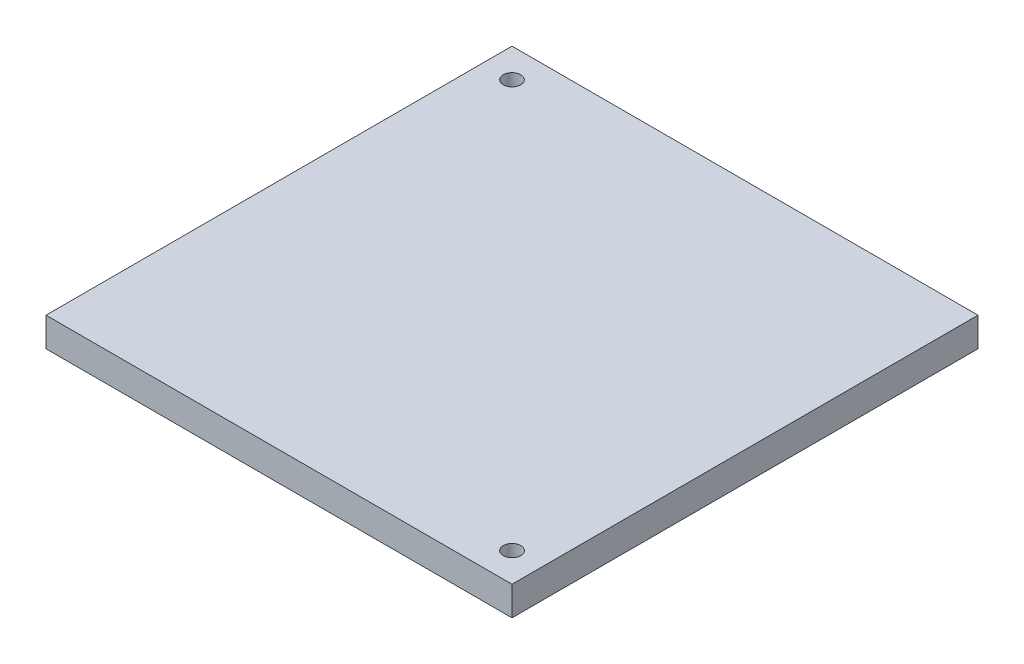
SolidWorks part; units mm, degrees
material "ABS PC"
ref_plane "Plan de face" through (0, 0, 0) normal (0, 0, 1) x (1, 0, 0)
ref_plane "Plan de dessus" through (0, 0, 0) normal (0, 1, 0) x (1, 0, 0)
ref_plane "Plan de droite" through (0, 0, 0) normal (1, 0, 0) x (0, 0, -1)
sketch "Esquisse1" plane through (0, 0, 0) normal (0, 1, 0) x (1, 0, 0)
  line L0 (-40, 40) -> (40, -40) construction
  line L1 (-40, 40) -> (40, 40)
  line L2 (-40, 40) -> (-40, -40)
  line L3 (-40, -40) -> (40, -40)
  line L4 (40, 40) -> (40, -40)
  dimension "D1" = 80
extrude "Boss.-Extru.1" add sketch "Esquisse1" along normal blind 5
sketch "Esquisse2" plane through (0, 5, 0) normal (0, 1, 0) x (1, 0, 0)
  line L0 (35, -35) -> (-35, 35) construction
  line L1 (-40, 40) -> (-40, -40) construction
  circle A0 centre (-35, 35) radius 1.5
  circle A1 centre (35, -35) radius 1.5
  dimension "D2" = 3
  dimension "D1" = 5
extrude "Enlèv. mat.-Extru.1" cut sketch "Esquisse2" against normal through all
